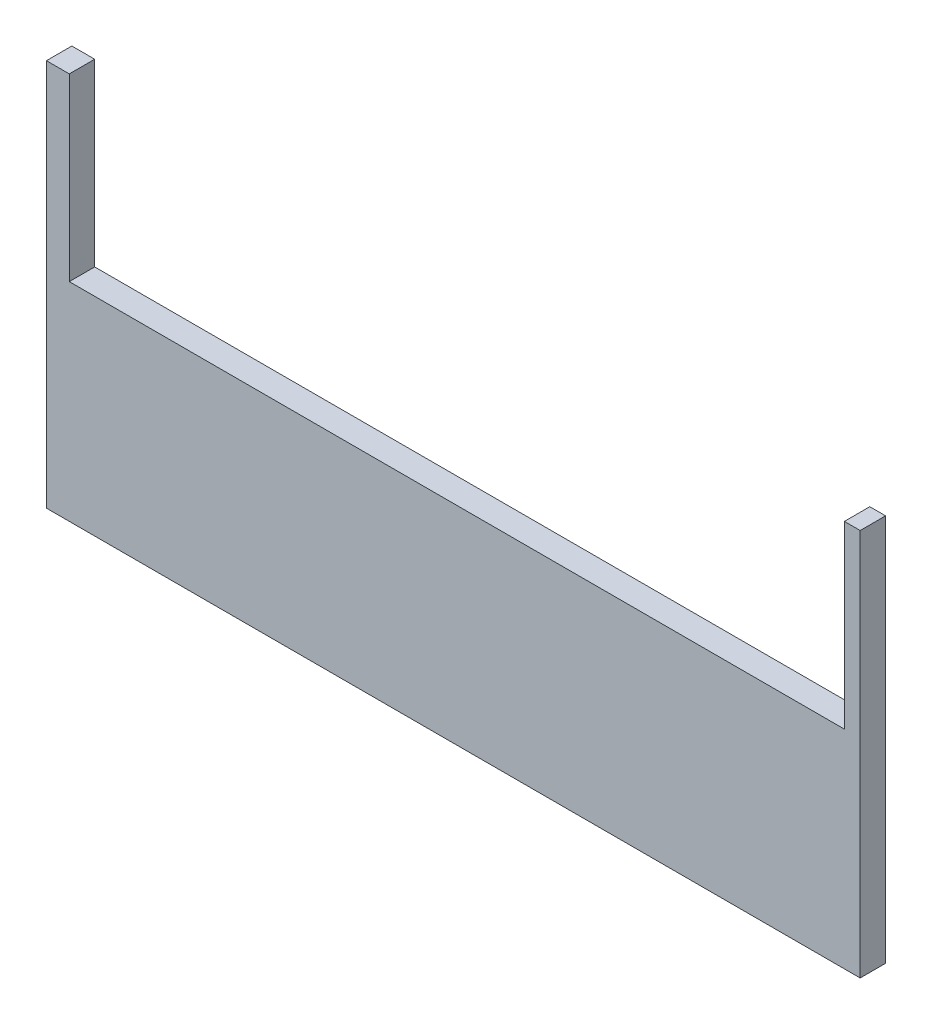
SolidWorks part; units mm, degrees
ref_plane "Front Plane" through (0, 0, 0) normal (0, 0, 1) x (1, 0, 0)
ref_plane "Top Plane" through (0, 0, 0) normal (0, 1, 0) x (1, 0, 0)
ref_plane "Right Plane" through (0, 0, 0) normal (1, 0, 0) x (0, 0, -1)
sketch "Sketch2" plane through (0, 0, 0) normal (0, 0, 1) x (1, 0, 0)
  line L1 (0, 0) -> (320, 0)
  line L2 (0, 0) -> (0, 152.4)
  line L3 (0, 152.4) -> (320, 152.4)
  line L4 (320, 0) -> (320, 152.4)
  dimension "D1" = 320
  dimension "D2" = 152.4
extrude "Boss-Extrude2" add sketch "Sketch2" along normal blind 10
sketch "Sketch7" plane through (0, 0, 10) normal (0, 0, 1) x (1, 0, 0)
  line L1 (313.7899, 81.6542) -> (8.9899, 81.6542)
  line L2 (313.7899, 81.6542) -> (313.7899, 157.034)
  line L3 (313.7899, 157.034) -> (8.9899, 157.034)
  line L4 (8.9899, 81.6542) -> (8.9899, 157.034)
  dimension "D1" = 304.8
extrude "Cut-Extrude1" cut sketch "Sketch7" against normal through all both and the other way through all
